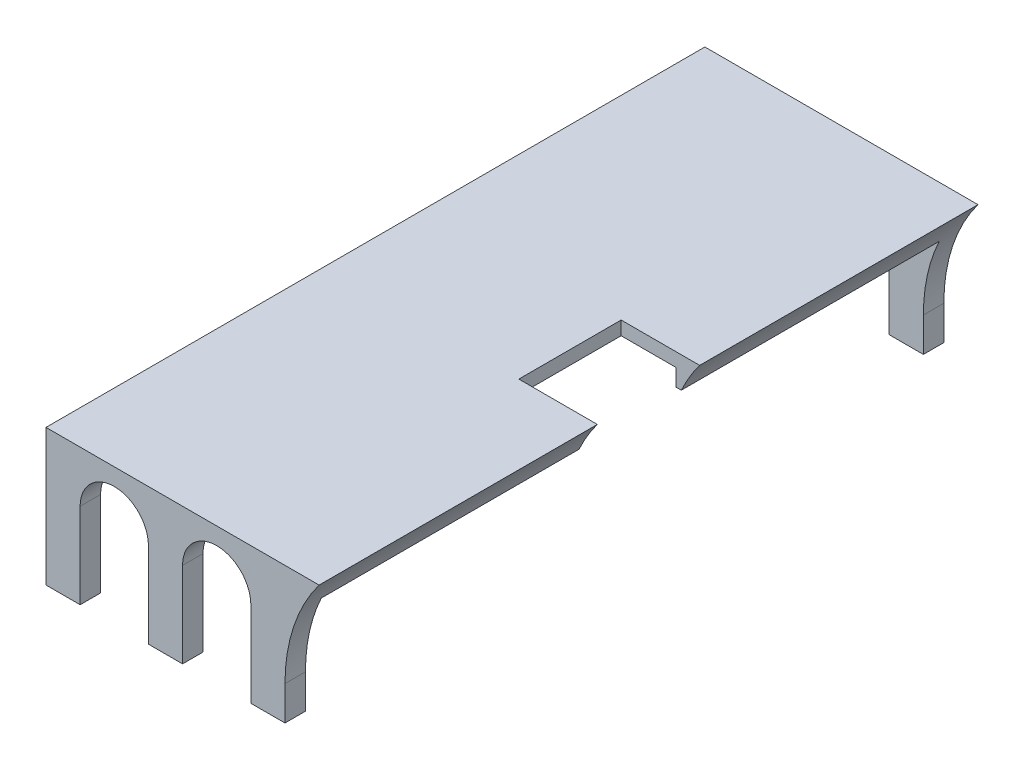
SolidWorks part; units mm, degrees
material "PTFE (general)"
ref_plane "Front Plane" through (0, 0, 0) normal (0, 0, 1) x (1, 0, 0)
ref_plane "Top Plane" through (0, 0, 0) normal (0, 1, 0) x (1, 0, 0)
ref_plane "Right Plane" through (0, 0, 0) normal (1, 0, 0) x (0, 0, -1)
sketch "Sketch8" plane through (0, 0, 0) normal (0, 0, 1) x (1, 0, 0)
  line L2 (-19.2614, -15.5669) -> (20.7386, -15.5669)
  line L3 (-19.2614, -15.5669) -> (-19.2614, -35.5669)
  line L4 (-19.2614, -35.5669) -> (20.7386, -35.5669)
  line L7 (20.7386, -15.5669) -> (20.7386, -35.5669)
  dimension "D1" = 40
  dimension "D2" = 20
extrude "Boss-Extrude1" add sketch "Sketch8" along normal mid plane 96.5 separate body
sketch "Sketch10" plane through (0, -35.5669, 0) normal (0, 1, 0) x (1, 0, 0)
  line L1 (-19.2614, -45.25) -> (17.2386, -45.25)
  line L2 (-19.2614, -45.25) -> (-19.2614, 45.25)
  line L3 (-19.2614, 45.25) -> (17.2386, 45.25)
  line L4 (17.2386, -45.25) -> (17.2386, 45.25)
  line L9 (20.7386, -48.25) -> (-19.2614, -48.25) construction
  line L10 (-19.2614, 48.25) -> (20.7386, 48.25) construction
  line L12 (-19.2614, -48.25) -> (-19.2614, 48.25) construction
  dimension "D1" = 3
  dimension "D2" = 3
  dimension "D3" = 36.5
extrude "Cut-Extrude6" cut sketch "Sketch10" along normal blind 18
sketch "Sketch12" plane through (20.7386, 0, 0) normal (1, 0, 0) x (0, 0, -1)
  line L0 (-48.25, -35.5669) -> (48.25, -35.5669) construction
  line L1 (-45.25, -20.0669) -> (45.25, -20.0669)
  line L2 (-45.25, -20.0669) -> (-45.25, -35.5669)
  line L3 (-45.25, -35.5669) -> (45.25, -35.5669)
  line L4 (45.25, -20.0669) -> (45.25, -35.5669)
  line L5 (-48.25, -35.5669) -> (-48.25, -15.5669) construction
  line L6 (-48.25, -15.5669) -> (48.25, -15.5669) construction
  line L7 (48.25, -35.5669) -> (48.25, -15.5669) construction
  dimension "D1" = 3
  dimension "D2" = 4.5
  dimension "D3" = 3
extrude "Cut-Extrude9" cut sketch "Sketch12" against normal blind 28
sketch "Sketch13" plane through (0, 0, 48.25) normal (0, 0, 1) x (1, 0, 0)
  line L4 (-19.2614, -35.5669) -> (20.7386, -35.5669) construction
  line L7 (15.7386, -35.5669) -> (20.7386, -35.5669)
  line L8 (20.7386, -35.5669) -> (20.7386, -15.5669)
  line L9 (15.7386, -30.5669) -> (15.7386, -35.5669)
  arc A0 (15.7386, -30.5669) -> (20.7386, -15.5669) centre (40.7386, -30.5669) cw
  dimension "D1" = 0
  dimension "D3" = 5
  dimension "D2" = 25
extrude "Cut-Extrude10" cut sketch "Sketch13" against normal through all
sketch "Sketch14" plane through (0, -15.5669, 0) normal (0, -1, 0) x (1, 0, 0)
  line L1 (9.2386, 7.5) -> (22.2386, 7.5)
  line L2 (9.2386, 7.5) -> (9.2386, -7.4857)
  line L3 (9.2386, -7.4857) -> (22.2386, -7.4857)
  line L4 (22.2386, 7.5) -> (22.2386, -7.4857)
extrude "Cut-Extrude11" cut sketch "Sketch14" along normal blind 10
fillet "Fillet6" radius 2.5 2 edges at (-1.0114, -17.5669, 45.25) (-1.0114, -17.5669, -45.25)
sketch "Sketch15" plane through (0, 0, 48.25) normal (0, 0, 1) x (1, 0, 0)
  line L0 (20.7386, -15.5669) -> (-19.2614, -15.5669) construction
  line L1 (-14.2614, -35.5669) -> (-4.2614, -35.5669)
  line L2 (-14.2614, -35.5669) -> (-14.2614, -23.0669)
  line L3 (-19.2614, -35.5669) -> (15.7386, -35.5669) construction
  line L4 (-4.2614, -35.5669) -> (-4.2614, -23.0669)
  line L5 (10.7386, -35.5669) -> (0.7386, -35.5669)
  line L6 (10.7386, -35.5669) -> (10.7386, -23.0669)
  line L7 (-19.2614, -15.5669) -> (-19.2614, -35.5669) construction
  line L8 (0.7386, -35.5669) -> (0.7386, -23.0669)
  arc A0 (-4.2614, -23.0669) -> (-14.2614, -23.0669) centre (-9.2614, -23.0669) ccw
  arc A1 (10.7386, -23.0669) -> (0.7386, -23.0669) centre (5.7386, -23.0669) ccw
  dimension "D6" = 5
  dimension "D7" = 7.5
  dimension "D5" = 5
  dimension "D1" = 10
  dimension "D2" = 5
  dimension "D3" = 5
  dimension "D4" = 10
extrude "Cut-Extrude12" cut sketch "Sketch15" against normal through all
